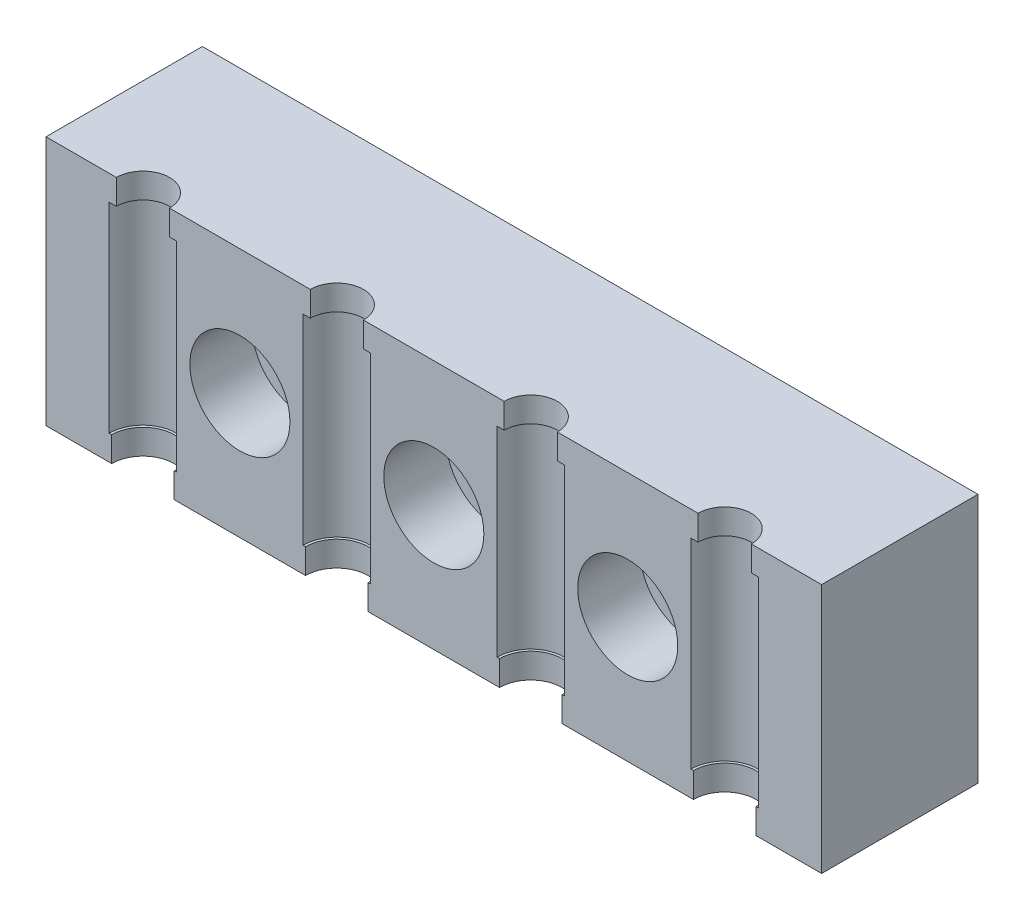
SolidWorks part; units mm, degrees
ref_plane "Plane1" through (0, 0, 0) normal (0, 0, 1) x (1, 0, 0)
ref_plane "Plane2" through (0, 0, 0) normal (0, 1, 0) x (1, 0, 0)
ref_plane "Plane3" through (0, 0, 0) normal (1, 0, 0) x (0, 0, -1)
sketch "Szkic1" plane through (0, 0, 0) normal (1, 0, 0) x (0, 0, -1)
  line L0 (0, 0) -> (0, -20)
  line L1 (0, 0) -> (13, 0)
  line L2 (13, 0) -> (13, -5)
  line L3 (13, -5) -> (15, -5)
  line L4 (15, -5) -> (15, -15)
  line L5 (15, -15) -> (13, -15)
  line L6 (13, -15) -> (13, -20)
  line L7 (0, -20) -> (13, -20)
extrude "Wyciągnięcie1" add sketch "Szkic1" along normal blind 62
sketch "Szkic2" plane through (0, 0, 0) normal (0, 1, 0) x (-1, 0, 0)
  line L0 (-62, 0) -> (0, 0) construction
  line L1 (0, -13) -> (0, 0) construction
  circle A0 centre (-7.75, 0) radius 2.125
  circle A1 centre (-23.25, 0) radius 2.125
  circle A2 centre (-38.75, 0) radius 2.125
  circle A3 centre (-54.25, 0) radius 2.125
  dimension "D1" = 7.75
  dimension "D2" = 4.25
extrude "Wytnij-wyciągnięcie1" cut sketch "Szkic2" against normal through all
ref_plane "Płaszczyzna1" through (0, -2, 0) normal (0, 1, 0) x (-1, 0, 0)
sketch "Szkic3" plane through (0, -2, 0) normal (0, 1, 0) x (-1, 0, 0)
  circle A0 centre (-7.75, 0) radius 2.7
  circle A1 centre (-23.25, 0) radius 2.7
  circle A2 centre (-38.75, 0) radius 2.7
  circle A3 centre (-54.25, 0) radius 2.7
  dimension "D1" = 5.4
extrude "Wytnij-wyciągnięcie2" cut sketch "Szkic3" against normal blind 16
sketch "Szkic4" plane through (0, 0, 0) normal (0, 1, 0) x (-1, 0, 0)
  line L0 (-62, -13) -> (0, -13) construction
  line L1 (-62, -15) -> (-57, -15)
  line L2 (-62, -15) -> (-62, -13)
  line L3 (-62, -13) -> (-57, -13)
  line L4 (-57, -15) -> (-57, -13)
  line L6 (0, -15) -> (-5, -15)
  line L7 (0, -15) -> (0, -13)
  line L8 (0, -13) -> (-5, -13)
  line L9 (-5, -15) -> (-5, -13)
  dimension "D1" = 5
  dimension "D2" = 5
extrude "Wytnij-wyciągnięcie3" cut sketch "Szkic4" against normal through all
chamfer "Sfazowanie1" distance 0.5 angle 45 8 edges at (57, -10, -15) (31, -5, -15) (5, -10, -15) (31, -15, -15) (31, -20, -13) (0, -10, -13) (31, 0, -13) (62, -10, -13)
sketch "Szkic5" plane through (0, 0, 0) normal (0, 0, 1) x (1, 0, 0)
  line L0 (41.45, -20) -> (25.95, -20) construction
  line L1 (62, 0) -> (62, -20) construction
  line L2 (56.95, -20) -> (41.45, -20) construction
  line L3 (25.95, -20) -> (10.45, -20) construction
  circle A0 centre (31, -10) radius 2.5
  circle A1 centre (46.5, -10) radius 2.5
  circle A2 centre (15.5, -10) radius 2.5
  dimension "D1" = 10
  dimension "D2" = 5
  dimension "D4" = 5
  dimension "D5" = 15.5
  dimension "D6" = 10
  dimension "D7" = 5
  dimension "D8" = 15.5
  dimension "D9" = 10
  dimension "D3" = 31
extrude "Wytnij-wyciągnięcie4" cut sketch "Szkic5" against normal through all
sketch "Szkic6" plane through (0, 0, 0) normal (0, 0, 1) x (1, 0, 0)
  circle A0 centre (46.5, -10) radius 4
  circle A1 centre (31, -10) radius 4
  circle A3 centre (15.5, -10) radius 4
  dimension "D1" = 8
  dimension "D2" = 8
  dimension "D3" = 8
extrude "Wytnij-wyciągnięcie5" cut sketch "Szkic6" against normal blind 5
sketch "Szkic7" plane through (0, -20, 0) normal (0, -1, 0) x (1, 0, 0)
  circle A0 centre (7.75, 0) radius 2.5
  circle A2 centre (23.25, 0) radius 2.5
  circle A3 centre (38.75, 0) radius 2.5
  circle A4 centre (54.25, 0) radius 2.5
  dimension "D1" = 5
extrude "Wytnij-wyciągnięcie6" cut sketch "Szkic7" against normal blind 10
